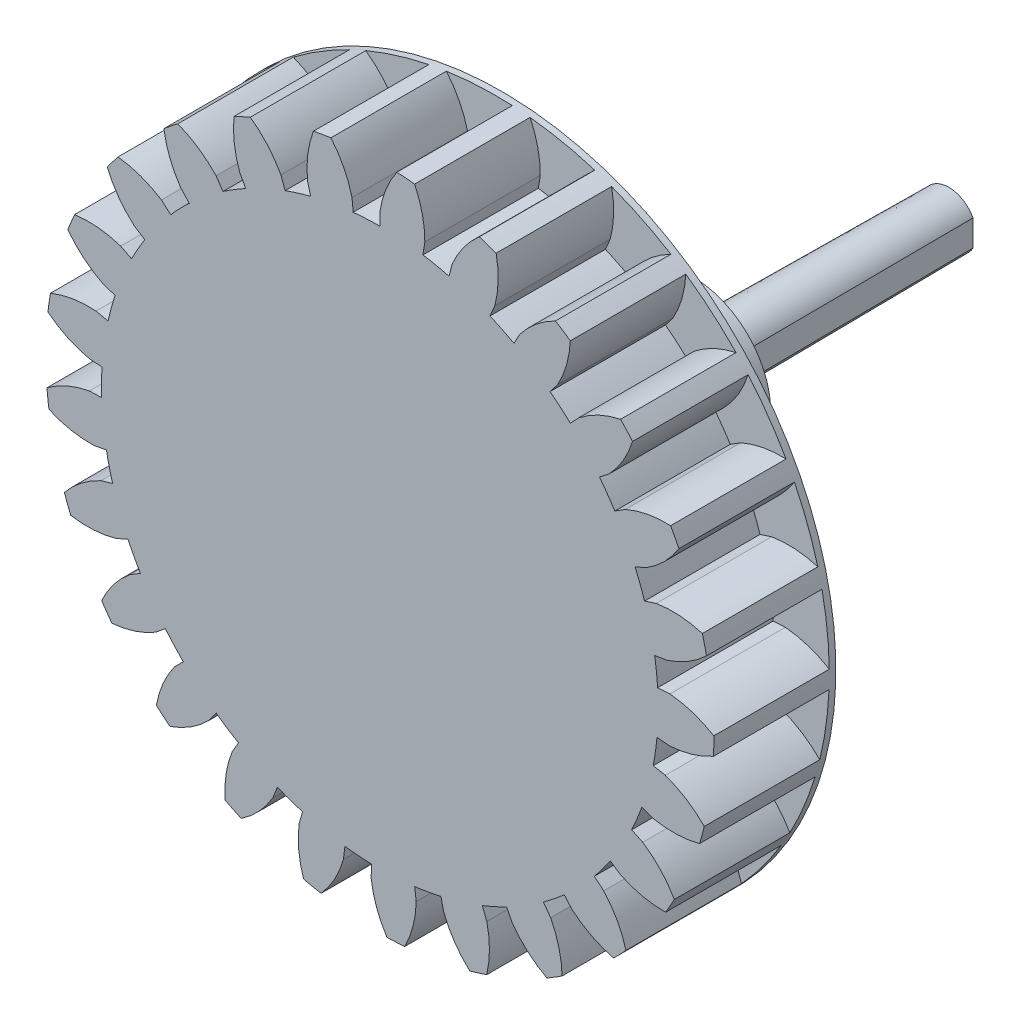
SolidWorks part; units mm, degrees
ref_plane "Front Plane" through (0, 0, 0) normal (0, 0, 1) x (1, 0, 0)
ref_plane "Top Plane" through (0, 0, 0) normal (0, 1, 0) x (1, 0, 0)
ref_plane "Right Plane" through (0, 0, 0) normal (1, 0, 0) x (0, 0, -1)
sketch "Sketch2" plane through (0, 0, 0) normal (0, 0, 1) x (1, 0, 0)
  circle A0 centre (0, 0) radius 20.25
  dimension "D1" = 40.5
extrude "gear outside diameter" add sketch "Sketch2" along normal blind 7
sketch "Sketch1" plane through (0, 0, 0) normal (0, 0, 1) x (1, 0, 0)
  line L0 (0, 17.6192) -> (0, 0) construction
  line L1 (0, 0) -> (0.2794, 18.7479) construction
  line L2 (0, 0) -> (1.0338, 20.2236) construction
  line L3 (0, 0) -> (-0.7463, 15.5587) construction
  line L4 (0, 17.6192) -> (0, 16.875)
  line L5 (-1.6863, 17.5384) -> (-1.6151, 16.7975)
  circle A0 centre (0, 0) radius 20.25 construction
  circle A1 centre (0, 0) radius 18.75 construction
  circle A2 centre (0, 0) radius 17.6192 construction
  arc A3 (1.0338, 20.2236) -> (0, 17.6192) centre (6.0814, 16.7125) ccw
  arc A4 (-2.9647, 20.0318) -> (-1.6863, 17.5384) centre (-7.653, 16.0537) cw
  arc A5 (-2.9647, 20.0318) -> (1.0338, 20.2236) centre (0, 0) cw
  arc A6 (0, 16.875) -> (-1.6151, 16.7975) centre (0, 0) ccw
  dimension "D1" = 40.5
  dimension "D2" = 37.5
  dimension "D3" = 35.2385
  dimension "D7" = 33.75
  dimension "D4" = 3.6
  dimension "D5" = 0.854
  dimension "D6" = 2.926
extrude "gear tooth cut" cut sketch "Sketch1" along normal through all
pattern_circular "gear teeth" count 25 over 360 about axis through (0, 0, 0) along (0, 0, 1) of "gear tooth cut"
sketch "Sketch3" plane through (0, 0, 0) normal (0, 0, 1) x (1, 0, 0)
  circle A0 centre (0, 0) radius 16.875
  dimension "D1" = 33.75
extrude "gear dedendum circle" add sketch "Sketch3" along normal up to surface (7 mm away) up to face at (0, 0, 7)
sketch "Sketch5" plane through (0, 0, 0) normal (0, 0, -1) x (-1, 0, 0)
  circle A0 centre (0, 0) radius 8
  dimension "D1" = 16
extrude "Boss-Extrude1" [suppressed] add sketch "Sketch5" along normal blind 1
sketch "Sketch4" plane through (0, 0, 7) normal (0, 0, 1) x (1, 0, 0)
  line L0 (-1.1832, -1.15) -> (1.1832, -1.15)
  arc A0 (1.1832, -1.15) -> (-1.1832, -1.15) centre (0, 0) ccw
  point P5 (0, 1.65)
  dimension "D1" = 3.3
  dimension "D2" = 2.8
extrude "Cut-Extrude1" [suppressed] cut sketch "Sketch4" against normal through all
chamfer "Chamfer1" [suppressed] distance 1.5 angle 45
chamfer "Chamfer2" [suppressed] distance 0.5 angle 45
sketch "Sketch8" plane through (0, 0, 0) normal (0, 0, -1) x (-1, 0, 0)
  circle A0 centre (0, 0) radius 4.7
  circle A2 centre (0, 0) radius 5 construction
  dimension "D1" = 0.3
  dimension "D2" = 10
extrude "Boss-Extrude3" add sketch "Sketch8" along normal blind 12
sketch "Sketch6" plane through (0, 0, -12) normal (0, 0, -1) x (-1, 0, 0)
  line L0 (1.6, 0.8246) -> (1.6, 0.6)
  line L1 (-1.6, 0.8246) -> (-1.6, -0.8246)
  line L2 (1.6, 0) -> (-1.6, 0) construction
  line L3 (1.6971, 0.6) -> (1.6971, -0.6)
  line L4 (1.6971, 0.6) -> (1.6, 0.6)
  line L5 (1.6971, -0.6) -> (1.6, -0.6)
  line L6 (1.6, -0.6) -> (1.6, -0.8246)
  line L7 (1.6, 0) -> (1.6971, 0) construction
  arc A0 (-1.6, -0.8246) -> (1.6, -0.8246) centre (0, 0) ccw
  arc A1 (1.6, 0.8246) -> (-1.6, 0.8246) centre (0, 0) ccw
  dimension "D1" = 3.6
  dimension "D2" = 3.2
  dimension "D3" = 1.2
extrude "Boss-Extrude2" add sketch "Sketch6" along normal blind 15.5 draft 0.5
sketch "Sketch9" plane through (0, 0, 0) normal (0, 0, -1) x (-1, 0, 0)
  circle A0 centre (0, 0) radius 20.25
  arc A1 (8.8368, 18.2201) -> (7.8532, 18.6652) centre (0, 0) ccw construction
extrude "Boss-Extrude4" add sketch "Sketch9" along normal blind 0.4
sketch "Sketch10" plane through (0, 0, 7) normal (0, 0, 1) x (1, 0, 0)
  circle A0 centre (0, 0) radius 13.875 construction
  arc A1 (-13.0024, -10.7565) -> (-11.9132, -11.9516) centre (0, 0) ccw construction
  circle A2 centre (-8.875, 0) radius 5
  circle A3 centre (0, 8.875) radius 5
  circle A4 centre (8.875, 0) radius 5
  circle A5 centre (0, -8.875) radius 5
  point P15 (0, 0)
  dimension "D1" = 3
  dimension "D3" = 10
  dimension "D2" = 4
extrude "Cut-Extrude2" [suppressed] cut sketch "Sketch10" against normal through all
sketch "Sketch7" plane through (0, 0, 7) normal (0, 0, 1) x (1, 0, 0)
  circle A0 centre (0, 0) radius 0.7141
equation "\"N\"= 25'Number of teeth"
equation "\"m\"= 1.5'module  (using 25.4/P for imperial gears)"
equation "\"F\"= 7'face width"
equation "\"phi\"=20 'pressure angle"
equation "\"d\"=\"N\"*\"m\""
equation "\"OD\"=(\"N\"+2)*\"m\""
equation "\"db\"=\"d\"* cos( \"phi\" ) "
equation "\"D5@Sketch1\"= (tan( \"phi\" )-\"phi\" * pi /180)*180/ pi "
equation "\"D2@Sketch1\" = \"d\""
equation "\"D3@Sketch1\"=\"db\""
equation "\"D1@Sketch1\"=\"OD\""
equation "\"phiB\"= arccos( \"db\"/\"OD\" ) "
equation "\"D6@Sketch1\"=tan(\"phiB\")*180 /  pi -\"phiB\""
equation "\"D4@Sketch1\" = 360/\"N\"/4"
equation "\"D1@Sketch2\" = \"OD\""
equation "\"D1@gear teeth\"=\"N\""
equation "\"x\"=2.5-\"N\"*(1-cos(\"phi\"))"
equation "\"D1@Sketch3\" = (\"N\"-2.5)*\"m\""
equation "\"D7@Sketch1\" = (\"N\"-2.5)*\"m\""
equation "\"D1@gear outside diameter\" = \"F\""
